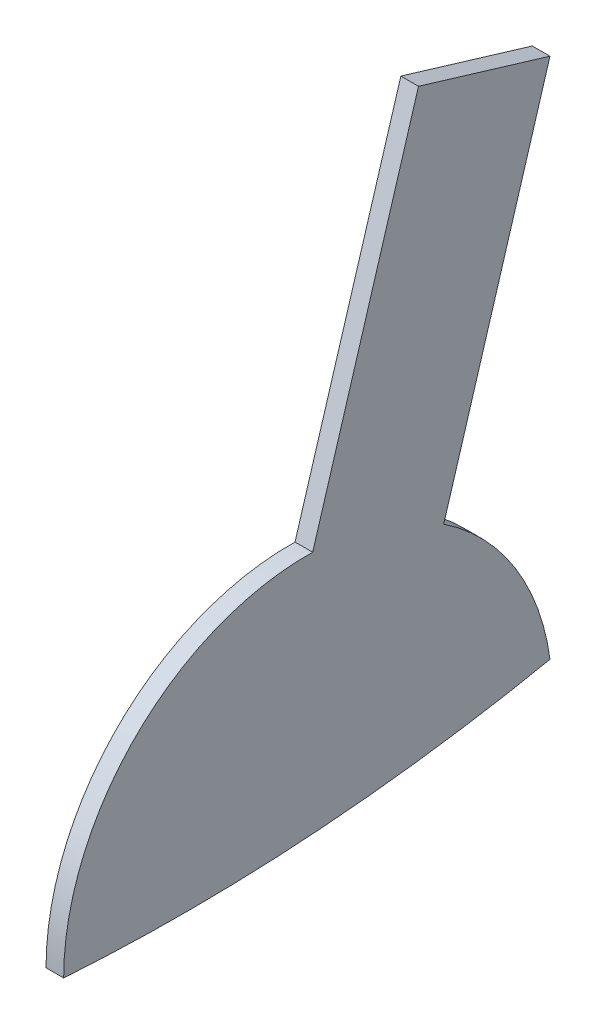
SolidWorks part; units mm, degrees
ref_plane "Front Plane" through (0, 0, 0) normal (0, 0, 1) x (1, 0, 0)
ref_plane "Top Plane" through (0, 0, 0) normal (0, 1, 0) x (1, 0, 0)
ref_plane "Right Plane" through (0, 0, 0) normal (1, 0, 0) x (0, 0, -1)
sketch "Sketch1"
  line L0 (-1.3155, -489.4818) -> (1511.3512, -489.4818) construction
  line L3 (1247.95, 0) -> (-1247.95, 0) construction
  line L4 (41.1404, 94.3547) -> (23.0765, 34.512)
  line L5 (41.1404, 94.3547) -> (18.7941, 101.1001)
  line L6 (0.806, 41.5085) -> (18.7941, 101.1001)
  arc A0 (41.1404, 5.5739) -> (23.0765, 34.512) centre (0, 0) ccw
  arc A1 (0.806, 41.5085) -> (-41.5163, 0) centre (0, 0) ccw
  spline S0 degree 2 poles (-41.5163, 0) (0.1879, -2.787) (41.1404, 5.5739) knots 0 0 0 1 1 1
  dimension "D2" = 62.2473
  dimension "D1" = 62.5096
extrude "Boss-Extrude1" add sketch "Sketch1" against normal mid plane 3
